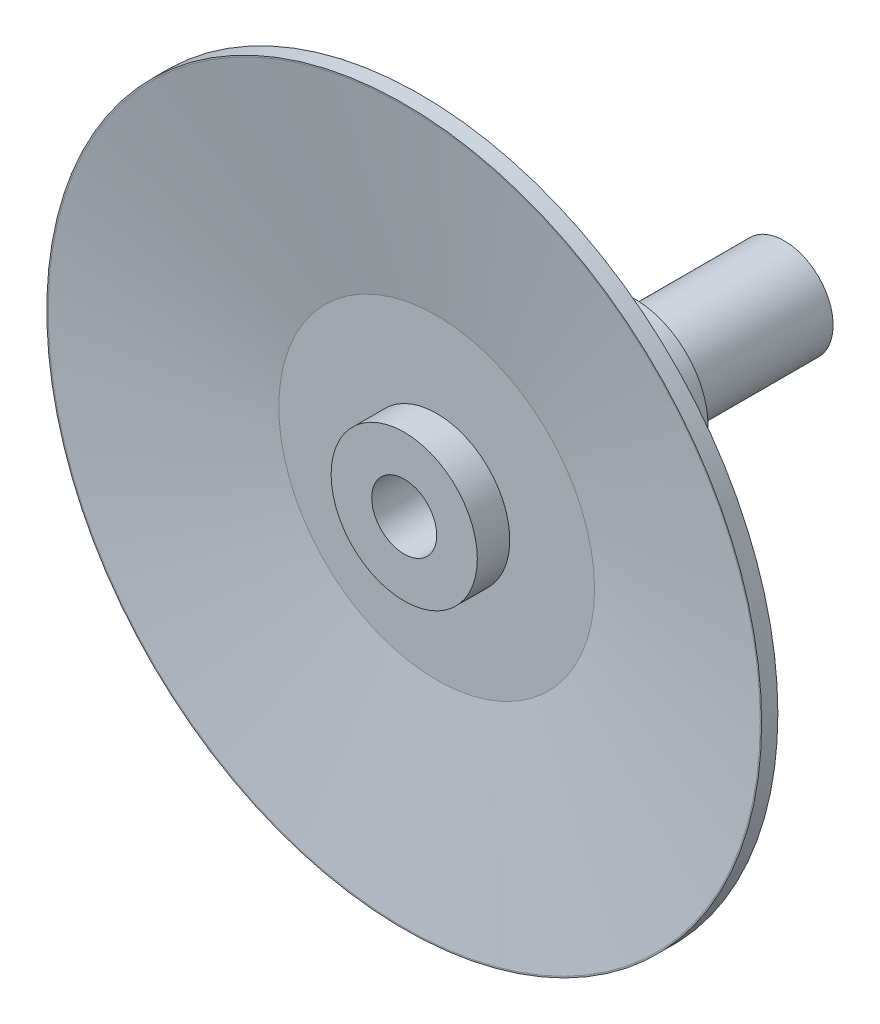
SolidWorks part; units mm, degrees
ref_plane "Front Plane" through (0, 0, 0) normal (0, 0, 1) x (1, 0, 0)
ref_plane "Top Plane" through (0, 0, 0) normal (0, 1, 0) x (1, 0, 0)
ref_plane "Right Plane" through (0, 0, 0) normal (1, 0, 0) x (0, 0, -1)
sketch "Sketch1" plane through (0, 0, 0) normal (0, 0, 1) x (1, 0, 0)
  circle A0 centre (0, 0) radius 22.5
  dimension "D1" = 45
extrude "Boss-Extrude1" add sketch "Sketch1" along normal blind 162
sketch "Sketch3" plane through (0, 0, 0) normal (1, 0, 0) x (0, 0, -1)
  line L1 (-162, 110) -> (-157, 110)
  line L2 (-157, 110) -> (-147, 49)
  line L3 (-147, 49) -> (-147, 22.5)
  line L4 (0, 22.5) -> (-162, 22.5) construction
  line L5 (-147, 22.5) -> (-162, 22.5)
  line L6 (-162, 0) -> (0, 0) construction
  line L8 (-162, 109.5929) -> (-152, 48.5929)
  line L9 (-152, 48.5929) -> (-152, 22.5)
  line L10 (-152, 48.5929) -> (-152, 22.5) construction
  line L11 (-161.9341, 109.1911) -> (-152, 48.5929) construction
  line L12 (-162, 109.5929) -> (-162, 110)
  point P10 (-152, 22.5)
  point P15 (-152, 30.676)
  point P16 (0, 0)
  point P17 (0, 0)
  point P18 (-162, 109.4431)
  point P20 (-162, 109.6353)
  dimension "D1" = 110
  dimension "D2" = 49
  dimension "D3" = 5
  dimension "D4" = 15
  dimension "D5" = 5
ref_axis "Axis1" through (0, 0, 162) along (0, 0, -1)
revolve "Revolve1" add sketch "Sketch3" angle 360 about axis through (0, 0, 162) along (0, 0, -1)
sketch "Sketch4" plane through (0, 0, 0) normal (0, 0, -1) x (-1, 0, 0)
  circle A0 centre (0, 0) radius 15
  circle A1 centre (0, 0) radius 22.5 construction
  circle A2 centre (0, 0) radius 22.5
  dimension "D1" = 30
extrude "Cut-Extrude1" cut sketch "Sketch4" against normal blind 91
sketch "Sketch5" plane through (0, 0, 0) normal (0, 0, -1) x (-1, 0, 0)
  circle A2 centre (0, 0) radius 15
  circle A3 centre (0, 0) radius 15
  dimension "D2" = 0
extrude "Cut-Extrude2" cut sketch "Sketch5" against normal blind 45
sketch "Sketch12" plane through (0, 0, 45) normal (0, 0, -1) x (-1, 0, 0)
  circle A2 centre (0, 0) radius 10
  circle A3 centre (0, 0) radius 10
  dimension "D1" = 5
extrude "Cut-Extrude3" cut sketch "Sketch12" against normal through all
sketch "Sketch13" plane through (0, 0, 45) normal (0, 0, -1) x (-1, 0, 0)
  line L0 (0, 0) -> (0, -10) construction
  line L1 (-1.5, -8.5) -> (1.5, -8.5)
  line L2 (-1.5, -8.5) -> (-1.5, -11.5)
  line L3 (-1.5, -11.5) -> (1.5, -11.5)
  line L4 (1.5, -8.5) -> (1.5, -11.5)
  line L5 (-1.5, -8.5) -> (1.5, -11.5) construction
  line L6 (-1.5, -11.5) -> (1.5, -8.5) construction
  point P0 (0, -10)
  point P5 (0, -10)
  dimension "D1" = 3
extrude "Cut-Extrude4" cut sketch "Sketch13" against normal blind 50
